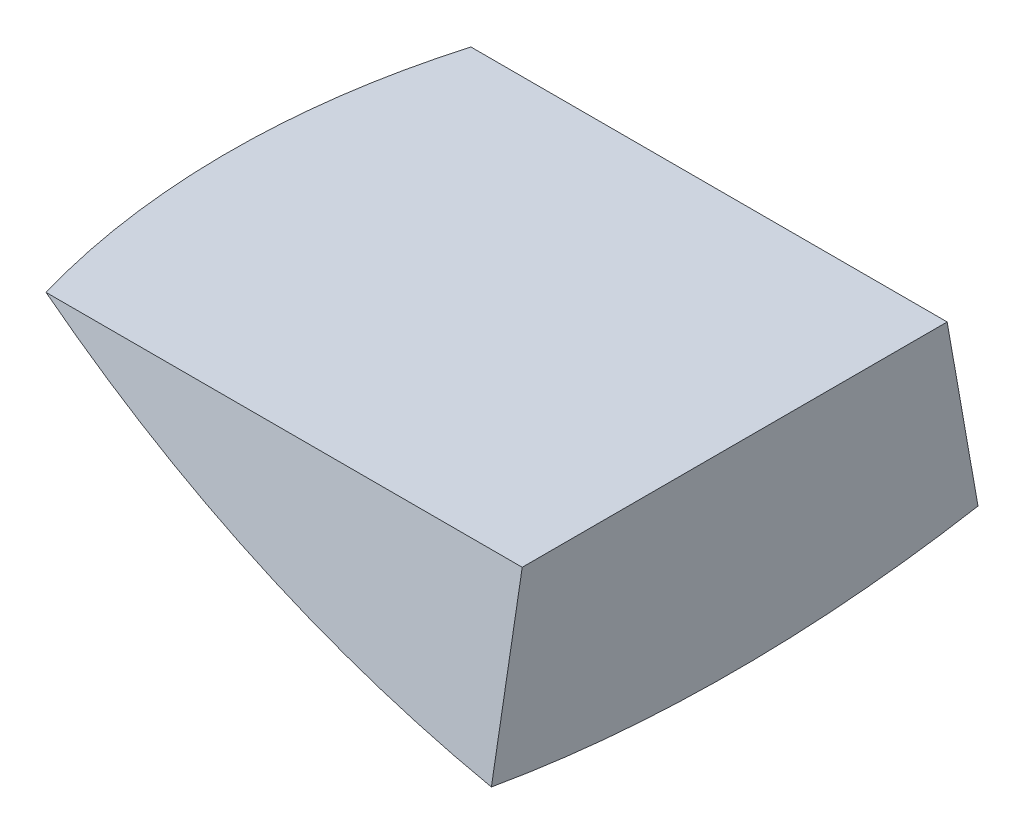
SolidWorks part; units mm, degrees
material "Polyurethane Foam Rigid"
ref_plane "Front Plane" through (0, 0, 0) normal (0, 0, 1) x (1, 0, 0)
ref_plane "Top Plane" through (0, 0, 0) normal (0, 1, 0) x (1, 0, 0)
ref_plane "Right Plane" through (0, 0, 0) normal (1, 0, 0) x (0, 0, -1)
sketch "Sketch1" plane through (0, 0, 0) normal (0, 0, 1) x (1, 0, 0)
  line L0 (-110.2666, -625.3529) -> (-110.2666, -523.7529)
  line L1 (0, 0) -> (0, -17.1989) construction
  line L2 (0, 0) -> (0, -324.9103) construction
  line L3 (0, 0) -> (-110.2666, -625.3529) construction
  line L4 (-110.2666, -523.7529) -> (-359.0374, -523.7529)
  line L5 (0, 0) -> (-376.3803, 0) construction
  line L6 (22.0533, 9.6471) -> (-365.6453, 9.6471) construction
  arc A0 (-110.2666, -625.3529) -> (-359.0374, -523.7529) centre (0, 0) cw
  dimension "D2" = 635
  dimension "D1" = 10
  dimension "D3" = 101.6
  dimension "D4" = 635
revolve "Revolve1" add sketch "Sketch1" angle 20 mid plane about L6
sketch "Sketch2" plane through (-110.2666, 0, 0) normal (1, 0, 0) x (0, 0, -1)
  line L1 (-217.2973, -505.5801) -> (197.3972, -505.5801)
  line L2 (-217.2973, -505.5801) -> (-217.2973, -536.4529)
  line L3 (-217.2973, -536.4529) -> (197.3972, -536.4529)
  line L4 (197.3972, -505.5801) -> (197.3972, -536.4529)
  arc A1 (-110.2666, -615.7058) -> (110.2666, -615.7058) centre (0, 9.6471) ccw construction
  point P4 (0, -625.3529)
  dimension "D1" = 88.9
extrude "Cut-Extrude1" cut sketch "Sketch2" against normal through all
equation "\"gapAngle\" = 10deg"
equation "\"D1@Sketch1\"=\"gapAngle\""
equation "\"LegFront\" = 25in"
equation "\"D2@Sketch1\"=\"LegFront\""
equation "\"LegSide\" = 25in"
equation "\"D4@Sketch1\"=\"LegSide\""
